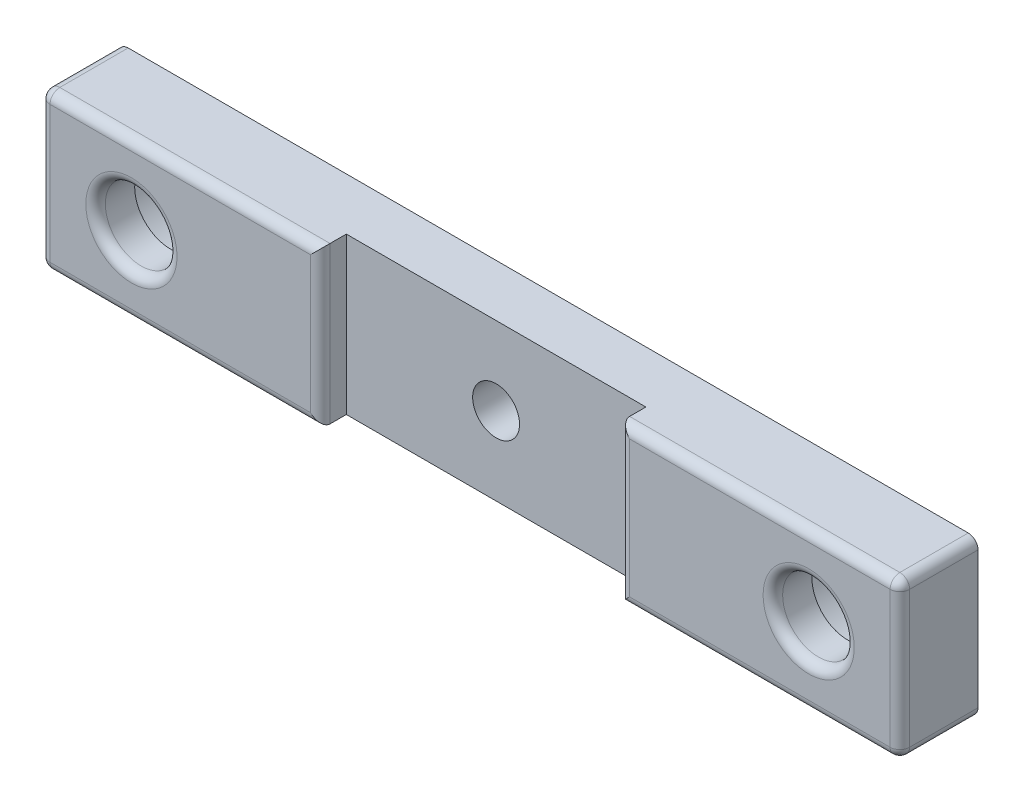
SolidWorks part; units mm, degrees
ref_plane "Plan de face" through (0, 0, 0) normal (0, 0, 1) x (1, 0, 0)
ref_plane "Plan de dessus" through (0, 0, 0) normal (0, 1, 0) x (1, 0, 0)
ref_plane "Plan de droite" through (0, 0, 0) normal (1, 0, 0) x (0, 0, -1)
sketch "Esquisse2" plane through (0, 0, 0) normal (0, 0, 1) x (1, 0, 0)
  line L1 (0, 0) -> (66, 0)
  line L2 (0, 0) -> (0, 12)
  line L3 (0, 12) -> (66, 12)
  line L4 (66, 0) -> (66, 12)
extrude "Boss.-Extru.1" add sketch "Esquisse2" along normal blind 6
sketch "Esquisse3" plane through (0, 0, 6) normal (0, 0, 1) x (1, 0, 0)
  line L1 (21.5, 0) -> (44.5, 0)
  line L2 (21.5, 0) -> (21.5, 12)
  line L3 (21.5, 12) -> (44.5, 12)
  line L4 (44.5, 0) -> (44.5, 12)
extrude "Enlèv. mat.-Extru.1" cut sketch "Esquisse3" against normal blind 2
sketch "Esquisse4" plane through (0, 0, 4) normal (0, 0, 1) x (1, 0, 0)
  circle A0 centre (33, 6) radius 1.8
extrude "Enlèv. mat.-Extru.2" cut sketch "Esquisse4" against normal through all
sketch "Esquisse5" plane through (0, 0, 0) normal (0, 0, -1) x (-1, 0, 0)
  circle A0 centre (-59, 6) radius 2.75
  circle A1 centre (-7, 6) radius 2.75
extrude "Enlèv. mat.-Extru.3" cut sketch "Esquisse5" against normal through all
sketch "Esquisse6" plane through (0, 0, 0) normal (0, 0, -1) x (-1, 0, 0)
  circle A0 centre (-59, 6) radius 5.1
  circle A1 centre (-7, 6) radius 5.1
extrude "Enlèv. mat.-Extru.4" cut sketch "Esquisse6" against normal blind 3
fillet "Congé1" radius 0.75 14 edges at (66, 6, 6) (55.25, 0, 6) (44.5, 6, 6) (55.25, 12, 6) (56.25, 6, 6) (0, 6, 6) (10.75, 12, 6) (21.5, 6, 6) (10.75, 0, 6) (4.25, 6, 6) (0, 12, 3) (0, 0, 3) (66, 0, 3) (66, 12, 3)
